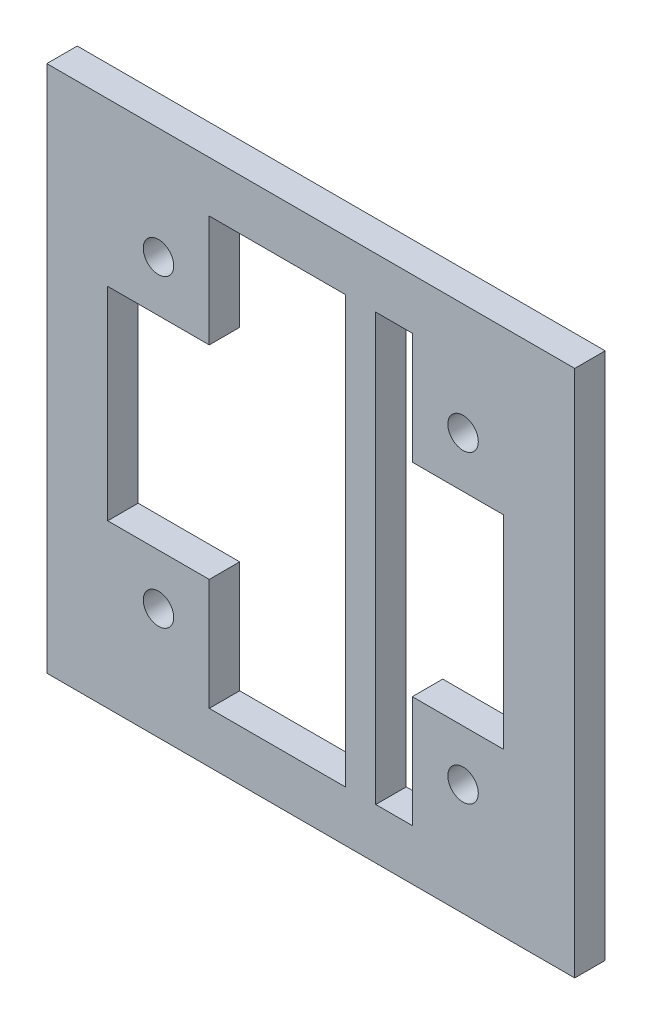
SolidWorks part; units mm, degrees
material "Resina de poliéster"
ref_plane "Alzado" through (0, 0, 0) normal (0, 0, 1) x (1, 0, 0)
ref_plane "Planta" through (0, 0, 0) normal (0, 1, 0) x (1, 0, 0)
ref_plane "Vista lateral" through (0, 0, 0) normal (1, 0, 0) x (0, 0, -1)
sketch "Model" plane through (0, 0, 0) normal (0, 0, 1) x (1, 0, 0)
  line L72 (92, 179) -> (92, 231)
  line L73 (40, 231) -> (40, 179)
  line L74 (40, 231) -> (40, 179)
  line L75 (40, 231) -> (92, 231)
  line L76 (92, 231) -> (92, 179)
  line L77 (40, 179) -> (92, 179)
  line L91 (49.5, 190) -> (52.5, 190)
  line L92 (51, 191.5) -> (51, 188.5)
  line L93 (81, 221.5) -> (81, 218.5)
  line L94 (79.5, 220) -> (82.5, 220)
  line L95 (49.5, 220) -> (52.5, 220)
  line L96 (51, 221.5) -> (51, 218.5)
  line L97 (81, 191.5) -> (81, 188.5)
  line L98 (79.5, 190) -> (82.5, 190)
  line L230 (46, 215) -> (46, 195)
  line L231 (56, 226) -> (56, 215)
  line L232 (46, 215) -> (56, 215)
  line L233 (46, 195) -> (56, 195)
  line L234 (56, 195) -> (56, 184)
  line L235 (56, 226) -> (56, 215)
  line L236 (69.4, 226) -> (69.4, 184)
  line L243 (85, 195) -> (85, 215)
  line L244 (76, 226) -> (76, 215)
  line L245 (76, 215) -> (85, 215)
  line L246 (76, 195) -> (85, 195)
  line L247 (76, 195) -> (76, 184)
  line L248 (72.4, 226) -> (72.4, 184)
  line L261 (56, 184) -> (69.4, 184)
  line L262 (56, 226) -> (69.4, 226)
  line L263 (72.4, 184) -> (76, 184)
  line L264 (72.4, 226) -> (76, 226)
  line L269 (72.4, 231) -> (72.4, 179) construction
  line L270 (69.4, 231) -> (69.4, 179) construction
  line L271 (43, 231) -> (43, 179) construction
  line L272 (46, 231) -> (46, 179) construction
  circle A108 centre (51, 220) radius 1.5
  circle A109 centre (81, 220) radius 1.5
  circle A110 centre (81, 190) radius 1.5
  circle A111 centre (51, 190) radius 1.5
  point P685 (51, 179)
  dimension "D2" = 52
  dimension "D3" = 3
  dimension "D4" = 19.6
  dimension "D5" = 11
extrude "Saliente-Extruir1" add sketch "Model" along normal blind 3 contours L73 L77 L72 L75 A111 A110 A109 A108 L231 L262 L236 L261 L234 L233 L230 L232 L248 L264 L244 L245 L243 L246 L247 L263
